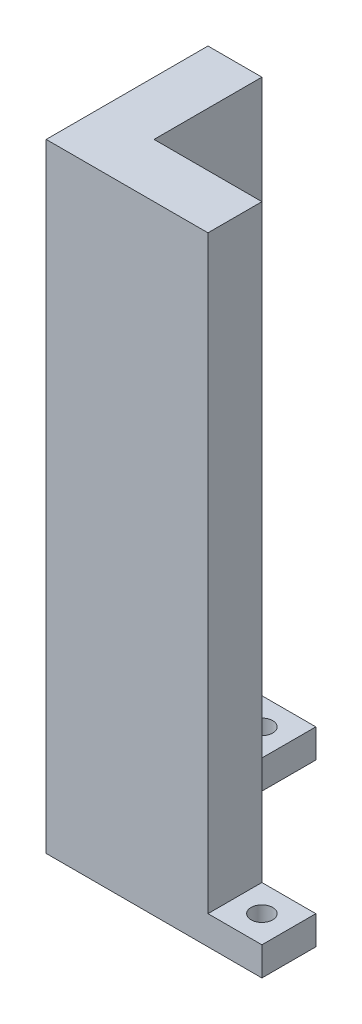
SolidWorks part; units mm, degrees
ref_plane "Front Plane" through (0, 0, 0) normal (0, 0, 1) x (1, 0, 0)
ref_plane "Top Plane" through (0, 0, 0) normal (0, 1, 0) x (1, 0, 0)
ref_plane "Right Plane" through (0, 0, 0) normal (1, 0, 0) x (0, 0, -1)
sketch "Sketch1" plane through (0, 0, 0) normal (0, 1, 0) x (1, 0, 0)
  line L0 (0, 0) -> (15, 0)
  line L1 (0, 15) -> (0, 22.5)
  line L2 (15, -7.5) -> (-7.5, -7.5)
  line L3 (-7.5, 22.5) -> (-7.5, -7.5)
  line L4 (22.5, 0) -> (22.5, -7.5)
  line L5 (0, 15) -> (0, 0)
  line L6 (15, -7.5) -> (22.5, -7.5)
  line L8 (22.5, 0) -> (15, 0)
  line L9 (0, 22.5) -> (-7.5, 22.5)
  circle A0 centre (-3.75, 18.75) radius 1.5
  circle A1 centre (18.75, -3.75) radius 1.5
extrude "Boss-Extrude1" add sketch "Sketch1" along normal blind 4
sketch "Sketch3" plane through (0, 4, 0) normal (0, 1, 0) x (1, 0, 0)
  line L0 (0, 0) -> (0, 22.5) construction
  line L1 (-7.5, 22.5) -> (-7.5, -7.5) construction
  line L2 (22.5, 0) -> (0, 0) construction
  line L3 (-7.5, -7.5) -> (22.5, -7.5) construction
  line L4 (0, 0) -> (0, 15)
  line L5 (-7.5, 15) -> (-7.5, -7.5)
  line L6 (15, 0) -> (0, 0)
  line L7 (-7.5, -7.5) -> (15, -7.5)
  line L10 (0, 15) -> (-7.5, 15)
  line L14 (15, 0) -> (15, -7.5)
extrude "Boss-Extrude2" add sketch "Sketch3" along normal blind 82
